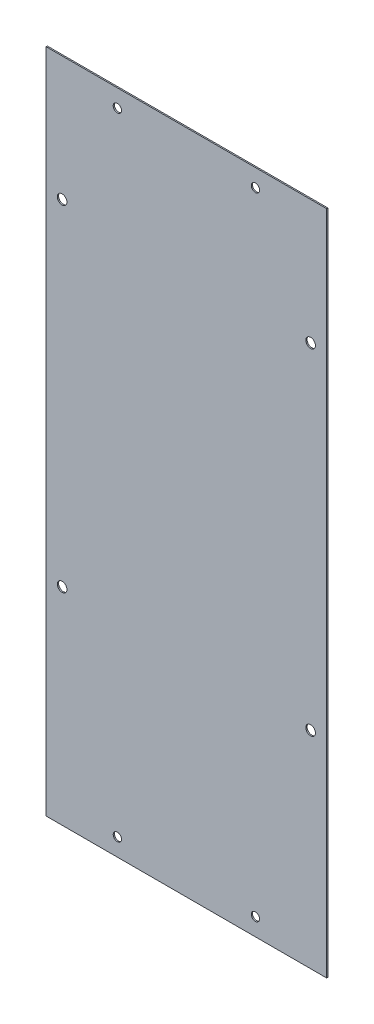
SolidWorks part; units mm, degrees
ref_plane "前视基准面" through (0, 0, 0) normal (0, 0, 1) x (1, 0, 0)
ref_plane "上视基准面" through (0, 0, 0) normal (0, 1, 0) x (1, 0, 0)
ref_plane "右视基准面" through (0, 0, 0) normal (1, 0, 0) x (0, 0, -1)
sketch "草图1" plane through (0, 0, 0) normal (0, 0, 1) x (1, 0, 0)
  line L1 (-101.6, -241.3) -> (101.6, -241.3)
  line L2 (-101.6, -241.3) -> (-101.6, 241.3)
  line L3 (-101.6, 241.3) -> (101.6, 241.3)
  line L4 (101.6, -241.3) -> (101.6, 241.3)
  line L5 (-101.6, -241.3) -> (101.6, 241.3) construction
  line L6 (-101.6, 241.3) -> (101.6, -241.3) construction
  point P0 (0, 0)
  dimension "D1" = 203.2
  dimension "D2" = 482.6
extrude "凸台-拉伸1" add sketch "草图1" along normal blind 0.9
sketch "草图2" plane through (0, 0, 0.9) normal (0, 0, 1) x (1, 0, 0)
  line L2 (101.6, 241.3) -> (-101.6, 241.3) construction
  line L3 (-90, 151.3) -> (90, 151.3) construction
  line L4 (-90, 151.3) -> (-90, -91.7) construction
  line L5 (-90, -91.7) -> (90, -91.7) construction
  line L6 (90, 151.3) -> (90, -91.7) construction
  line L7 (0, -91.7) -> (0, 151.3) construction
  line L8 (-90, 29.8) -> (90, 29.8) construction
  circle A0 centre (-90, 151.3) radius 3.5
  circle A1 centre (90, 151.3) radius 3.5
  circle A2 centre (90, -91.7) radius 3.5
  circle A3 centre (-90, -91.7) radius 3.5
  point P41 (0, 29.8)
  dimension "D1" = 243
  dimension "D2" = 180
  dimension "D3" = 0
  dimension "D4" = 90
extrude "切除-拉伸1" cut sketch "草图2" against normal blind 0.9
sketch "草图3" plane through (0, 0, 0.9) normal (0, 0, 1) x (1, 0, 0)
  line L1 (-50, 228.6) -> (50, 228.6) construction
  line L2 (-50, 228.6) -> (-50, -228.6) construction
  line L3 (-50, -228.6) -> (50, -228.6) construction
  line L4 (50, 228.6) -> (50, -228.6) construction
  line L5 (-50, 228.6) -> (50, -228.6) construction
  line L6 (-50, -228.6) -> (50, 228.6) construction
  circle A0 centre (-50, 228.6) radius 3
  circle A1 centre (50, 228.6) radius 3
  circle A2 centre (50, -228.6) radius 3
  circle A3 centre (-50, -228.6) radius 3
  point P0 (0, 0)
extrude "切除-拉伸2" cut sketch "草图3" against normal blind 0.9
